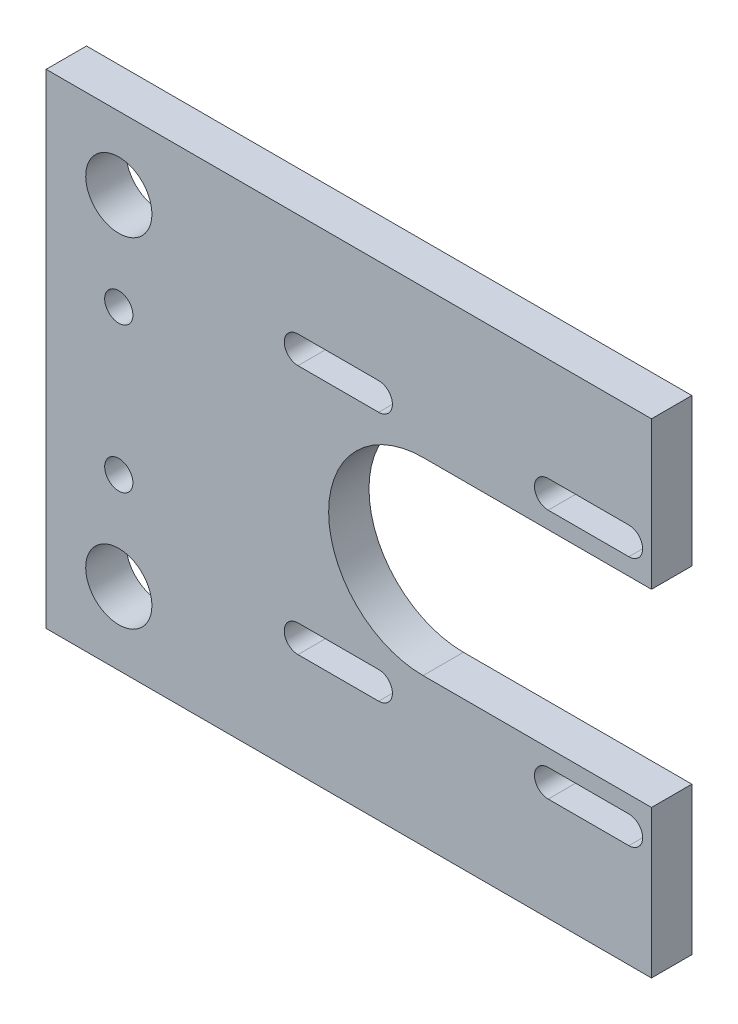
SolidWorks part; units mm, degrees
ref_plane "Front Plane" through (0, 0, 0) normal (0, 0, 1) x (1, 0, 0)
ref_plane "Top Plane" through (0, 0, 0) normal (0, 1, 0) x (1, 0, 0)
ref_plane "Right Plane" through (0, 0, 0) normal (1, 0, 0) x (0, 0, -1)
sketch "Sketch1" plane through (0, 0, 0) normal (1, 0, 0) x (0, 0, -1)
  line L1 (-38.6073, 28.2554) -> (-33.6073, 28.2554)
  line L2 (-38.6073, 28.2554) -> (-38.6073, -31.7446)
  line L3 (-38.6073, -31.7446) -> (-33.6073, -31.7446)
  line L4 (-33.6073, 28.2554) -> (-33.6073, -31.7446)
  dimension "D1" = 60
  dimension "D2" = 5
extrude "Boss-Extrude1" add sketch "Sketch1" along normal blind 5
sketch "Sketch2" plane through (5, 0, 0) normal (1, 0, 0) x (0, 0, -1)
  line L0 (-38.6073, -31.7446) -> (-33.6073, -31.7446) construction
  line L1 (-38.6073, 28.2554) -> (-33.6073, 28.2554)
  line L2 (-38.6073, 28.2554) -> (-38.6073, -31.7446)
  line L3 (-38.6073, -31.7446) -> (-33.6073, -31.7446)
  line L4 (-33.6073, 28.2554) -> (-33.6073, -31.7446)
  dimension "D1" = 5
extrude "Boss-Extrude2" add sketch "Sketch2" along normal blind 50
sketch "Sketch5" plane through (0, 0, 33.6073) normal (0, 0, -1) x (-1, 0, 0)
  line L2 (-26.7, -1.7446) -> (-56.7, -1.7446) construction
  line L3 (-26.7, -13.4446) -> (-56.7, -13.4446)
  line L4 (-26.7, 9.9554) -> (-56.7, 9.9554)
  arc A1 (-26.7, -13.4446) -> (-26.7, 9.9554) centre (-26.7, -1.7446) ccw
  arc A2 (-56.7, 9.9554) -> (-56.7, -13.4446) centre (-56.7, -1.7446) ccw
  point P6 (-41.7, -1.7446)
extrude "Cut-Extrude4" cut sketch "Sketch5" against normal through all
sketch "Sketch6" plane through (0, 0, 33.6073) normal (0, 0, -1) x (-1, 0, 0)
  line L0 (-42.2, 13.7554) -> (-52.2, 13.7554) construction
  line L1 (-42.2, 12.0554) -> (-52.2, 12.0554)
  line L2 (-42.2, 15.4554) -> (-52.2, 15.4554)
  line L4 (-42.2, -17.2446) -> (-52.2, -17.2446) construction
  line L5 (-42.2, -18.9446) -> (-52.2, -18.9446)
  line L6 (-42.2, -15.5446) -> (-52.2, -15.5446)
  line L7 (-11.2, -17.2446) -> (-21.2, -17.2446) construction
  line L8 (-11.2, -18.9446) -> (-21.2, -18.9446)
  line L9 (-11.2, -15.5446) -> (-21.2, -15.5446)
  line L10 (-11.2, 13.7554) -> (-21.2, 13.7554) construction
  line L11 (-11.2, 12.0554) -> (-21.2, 12.0554)
  line L12 (-11.2, 15.4554) -> (-21.2, 15.4554)
  arc A1 (-42.2, -18.9446) -> (-42.2, -15.5446) centre (-42.2, -17.2446) ccw
  arc A2 (-52.2, -15.5446) -> (-52.2, -18.9446) centre (-52.2, -17.2446) ccw
  arc A3 (-11.2, -18.9446) -> (-11.2, -15.5446) centre (-11.2, -17.2446) ccw
  arc A5 (-42.2, 12.0554) -> (-42.2, 15.4554) centre (-42.2, 13.7554) ccw
  arc A6 (-52.2, 15.4554) -> (-52.2, 12.0554) centre (-52.2, 13.7554) ccw
  arc A8 (-21.2, -15.5446) -> (-21.2, -18.9446) centre (-21.2, -17.2446) ccw
  arc A9 (-11.2, 12.0554) -> (-11.2, 15.4554) centre (-11.2, 13.7554) ccw
  arc A10 (-21.2, 15.4554) -> (-21.2, 12.0554) centre (-21.2, 13.7554) ccw
  arc A11 (-26.7, -13.4446) -> (-26.7, 9.9554) centre (-26.7, -1.7446) ccw construction
  point P1 (-47.2, -17.2446)
  point P2 (-47.2, 13.7554)
  point P16 (-16.2, -17.2446)
  point P23 (-16.2, 13.7554)
  dimension "D1" = 15.5
  dimension "D3" = 15.5
  dimension "D4" = 15.5
  dimension "D2" = 15.5
  dimension "D5" = 15.5
  dimension "D6" = 15.5
extrude "Cut-Extrude5" cut sketch "Sketch6" against normal through all
sketch "Sketch7" plane through (0, 0, 0) normal (-1, 0, 0) x (0, 0, 1)
  line L1 (33.6073, 28.2554) -> (38.6073, 28.2554)
  line L2 (33.6073, 28.2554) -> (33.6073, -31.7446)
  line L3 (33.6073, -31.7446) -> (38.6073, -31.7446)
  line L4 (38.6073, 28.2554) -> (38.6073, -31.7446)
extrude "Boss-Extrude3" add sketch "Sketch7" along normal blind 20
sketch "Sketch8" plane through (0, 0, 33.6073) normal (0, 0, -1) x (-1, 0, 0)
  line L0 (20, 28.2554) -> (20, -31.7446) construction
  line L1 (-55, -31.7446) -> (20, -31.7446) construction
  line L2 (-55, 28.2554) -> (20, 28.2554) construction
  circle A0 centre (11, 19.2554) radius 4.1
  circle A1 centre (11, -22.7446) radius 4.1
  circle A2 centre (11, -10.7446) radius 1.75
  circle A3 centre (11, 7.2554) radius 1.75
  dimension "D1" = 9
  dimension "D2" = 9
  dimension "D3" = 9
  dimension "D4" = 9
  dimension "D5" = 9
  dimension "D6" = 9
  dimension "D7" = 21
  dimension "D8" = 18
extrude "Cut-Extrude6" cut sketch "Sketch8" against normal through all
